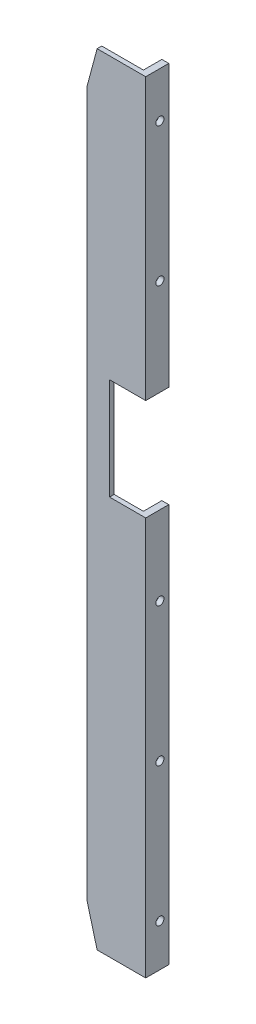
SolidWorks part; units mm, degrees
material "6061-T6 Al"
ref_plane "Front" through (0, 0, 0) normal (0, 0, 1) x (1, 0, 0)
ref_plane "Top" through (0, 0, 0) normal (0, 1, 0) x (1, 0, 0)
ref_plane "Right" through (0, 0, 0) normal (1, 0, 0) x (0, 0, -1)
sketch "MASS SEPARATION" plane through (0, 0, 0) normal (0, 0, 1) x (1, 0, 0)
  line L0 (334.7121, 0) -> (0, 0) construction
  line L1 (0, 0) -> (0, -602) construction
  line L2 (0, -602) -> (334.7121, -602) construction
  line L3 (163.2291, 47.5) -> (163.2291, -47.5)
  line L4 (163.2291, -554.5) -> (163.2291, -649.5)
  line L5 (-163.2291, -554.5) -> (-163.2291, -649.5)
  line L6 (-163.2291, 47.5) -> (-163.2291, -47.5)
  line L7 (168.2291, 47.5) -> (-168.2291, 47.5) construction
  line L8 (168.2291, 47.5) -> (168.2291, -649.5) construction
  line L9 (168.2291, -649.5) -> (-168.2291, -649.5) construction
  line L10 (-168.2291, -649.5) -> (-168.2291, 47.5) construction
  line L11 (0, -301) -> (297.114, -301) construction
  line L12 (-154.0291, -234.7) -> (-154.0291, -288.5)
  line L13 (6.2291, -234.7) -> (154.0291, -234.7)
  line L14 (6.2291, -234.7) -> (6.2291, -288.5)
  line L15 (6.2291, -288.5) -> (154.0291, -288.5)
  line L16 (154.0291, -234.7) -> (154.0291, -288.5)
  line L17 (-6.2291, -288.5) -> (-154.0291, -288.5)
  line L18 (-6.2291, -234.7) -> (-6.2291, -288.5)
  line L19 (-6.2291, -234.7) -> (-154.0291, -234.7)
  arc A0 (163.2291, 47.5) -> (-163.2291, 47.5) centre (0, 0) ccw
  arc A1 (163.2291, -554.5) -> (-163.2291, -554.5) centre (0, -602) ccw
  arc A2 (-163.2291, -47.5) -> (163.2291, -47.5) centre (0, 0) ccw
  arc A3 (-163.2291, -649.5) -> (163.2291, -649.5) centre (0, -602) ccw
  point P13 (168.2291, 47.5)
  point P14 (168.2291, -649.5)
  point P15 (-168.2291, 47.5)
  point P16 (-168.2291, -649.5)
  dimension "D2" = 170
  dimension "D1" = 602
  dimension "D3" = 95
  dimension "D4" = 12.5
  dimension "D5" = 5
  dimension "D6" = 301
  dimension "D7" = 5
  dimension "D8" = 147.8
  dimension "D9" = 162
  dimension "D10" = 53.8
  dimension "D11" = 301
  dimension "D12" = 234.7
  dimension "D13" = 326.4583
sketch "Sketch2" plane through (0, 0, 0) normal (0, 0, 1) x (1, 0, 0)
  line L0 (168.2291, 47.5) -> (168.2291, -47.5)
  line L1 (168.2291, 47.5) -> (204.0291, 47.5)
  line L2 (154.0291, -234.7) -> (154.0291, -288.5) construction
  line L3 (163.2291, 47.5) -> (163.2291, -47.5) construction
  line L4 (204.0291, 47.5) -> (204.0291, -649.5)
  line L5 (0, 0) -> (283.1149, 0) construction
  line L6 (334.7121, 0) -> (0, 0) construction
  line L7 (0, -602) -> (334.7121, -602) construction
  line L8 (168.2291, -554.5) -> (168.2291, -649.5)
  line L9 (168.2291, -649.5) -> (204.0291, -649.5)
  line L10 (159.0291, -81.8349) -> (159.0291, -520.1651)
  line L13 (168.2291, -47.5) -> (159.0291, -81.8349)
  line L14 (168.2291, -554.5) -> (159.0291, -520.1651)
  dimension "D1" = 47.5
  dimension "D2" = 5
  dimension "D3" = 45
  dimension "D4" = 5
  dimension "D5" = 47.5
  dimension "D6" = 47.5
  dimension "D7" = 15
  dimension "D8" = 47.5
  dimension "D9" = 15
  dimension "D10" = 697
extrude "Extrude1" add sketch "Sketch2" along normal mid plane 101.6
sketch "Sketch3" plane through (0, 0, 0) normal (0, 1, 0) x (1, 0, 0)
  line L1 (142.5291, 49.3) -> (202.5291, 49.3)
  line L2 (142.5291, 49.3) -> (142.5291, -49.3)
  line L3 (142.5291, -49.3) -> (202.5291, -49.3)
  line L4 (202.5291, 49.3) -> (202.5291, -49.3)
  line L5 (204.0291, 50.8) -> (168.2291, 50.8) construction
  line L6 (204.0291, -50.8) -> (204.0291, 50.8) construction
  line L7 (204.0291, -50.8) -> (168.2291, -50.8) construction
  dimension "D1" = 1.5
  dimension "D2" = 1.5
  dimension "D3" = 1.5
  dimension "D4" = 60
extrude "Cut-Extrude1" cut sketch "Sketch3" against normal through all and the other way through all
ref_plane "Plane1" through (0, -301, 0) normal (0, 1, 0) x (-1, 0, 0)
sketch "Sketch5" plane through (0, -301, 0) normal (0, 1, 0) x (1, 0, 0)
  line L0 (159.0291, 49.3) -> (159.0291, 50.8) construction
  line L1 (198.0291, 13.4125) -> (202.5291, 13.4125)
  line L2 (164.5291, 1.4125) -> (164.5291, -1.5875)
  line L3 (164.5291, -1.5875) -> (202.5291, -1.5875)
  line L4 (202.5291, 13.4125) -> (202.5291, -1.5875)
  line L6 (-163.2291, 0) -> (163.2291, 0) construction
  line L7 (202.5291, -49.3) -> (202.5291, 49.3) construction
  line L8 (198.0291, 13.4125) -> (198.0291, 1.4125)
  line L9 (198.0291, 1.4125) -> (164.5291, 1.4125)
  dimension "D1" = 15
  dimension "D2" = 38
  dimension "D3" = 1.5875
  dimension "D4" = 3
  dimension "D5" = 4.5
  dimension "D6" = 5.5
extrude "Extrude2" add sketch "Sketch5" along normal offset from surface 95 and the other way offset from surface (253.5 mm away) 95 separate body up to face at (185.7541, 47.5, 0) other way up to face at (185.7541, -649.5, 0)
sketch "Sketch11" plane through (0, 0, 0) normal (0, 0, 1) x (1, 0, 0)
  line L0 (170.9739, -47.5) -> (153.9591, -111)
  line L1 (153.9591, -111) -> (130.0291, -111)
  line L2 (130.0291, -111) -> (130.0291, -11)
  line L3 (170.9739, -47.5) -> (170.9739, -11)
  line L5 (170.9739, -11) -> (130.0291, -11)
  line L9 (23.4911, -301) -> (267.2307, -301) construction
  line L10 (0, -301) -> (297.114, -301) construction
  line L11 (153.9591, -491) -> (130.0291, -491)
  line L12 (170.9739, -554.5) -> (153.9591, -491)
  line L13 (170.9739, -554.5) -> (170.9739, -591)
  line L14 (170.9739, -591) -> (130.0291, -591)
  line L15 (130.0291, -491) -> (130.0291, -591)
  line L16 (159.0291, -81.8349) -> (159.0291, -520.1651) construction
  dimension "D1" = 290
  dimension "D2" = 100
  dimension "D3" = 29
  dimension "D4" = 23.93
extrude "Extrude8" cut sketch "Sketch11" against normal mid plane 150
sketch "Sketch4" plane through (0, 0, 0) normal (0, 0, 1) x (1, 0, 0)
  line L0 (159.0291, -81.8349) -> (159.0291, -520.1651) construction
  line L1 (209.0291, -229.7) -> (179.0291, -229.7)
  line L2 (209.0291, -229.7) -> (209.0291, -295.7)
  line L3 (209.0291, -295.7) -> (179.0291, -295.7)
  line L4 (179.0291, -229.7) -> (179.0291, -295.7)
  line L6 (164.5291, -71.5522) -> (164.5291, -530.4478) construction
  line L7 (6.2291, -234.7) -> (154.0291, -234.7) construction
  line L8 (6.2291, -288.5) -> (154.0291, -288.5) construction
  line L9 (204.0291, -649.5) -> (204.0291, 47.5) construction
  dimension "D1" = 5
  dimension "D2" = 7.2
  dimension "D3" = 5
  dimension "D4" = 20
  dimension "D5" = 66
  dimension "D6" = 14.5
extrude "Cut-Extrude2" cut sketch "Sketch4" against normal mid plane 92
sketch "Sketch7" plane through (0, 0, 0) normal (0, 0, 1) x (1, 0, 0)
  line L0 (159.0291, -81.8349) -> (159.0291, -520.1651) construction
  line L1 (129.0291, -157.5) -> (179.0291, -157.5)
  line L2 (129.0291, -157.5) -> (129.0291, -197.5)
  line L3 (129.0291, -197.5) -> (179.0291, -197.5)
  line L4 (179.0291, -157.5) -> (179.0291, -197.5)
  line L5 (129.0291, -414.5) -> (179.0291, -414.5)
  line L6 (129.0291, -414.5) -> (129.0291, -454.5)
  line L7 (129.0291, -454.5) -> (179.0291, -454.5)
  line L8 (179.0291, -414.5) -> (179.0291, -454.5)
  line L11 (168.2291, -649.5) -> (204.0291, -649.5) construction
  line L13 (204.0291, 47.5) -> (168.2291, 47.5) construction
  dimension "D1" = 20
  dimension "D2" = 50
  dimension "D3" = 40
  dimension "D4" = 40
  dimension "D5" = 235
  dimension "D6" = 245
  dimension "D7" = 20
extrude "Extrude4" [suppressed] cut sketch "Sketch7" against normal mid plane 150
sketch "Sketch8" plane through (0, 0, -50.8) normal (0, 0, -1) x (-1, 0, 0)
  line L0 (-227.5077, -262.7) -> (-137.1127, -262.7) construction
  line L1 (-204.0291, 47.5) -> (-168.2291, 47.5) construction
  line L2 (-204.0291, -649.5) -> (-204.0291, 47.5) construction
  circle A0 centre (-190.8541, -239.7) radius 2.25
  circle A1 centre (-190.8541, -285.7) radius 2.25
  dimension "D1" = 4.5
  dimension "D2" = 310.2
  dimension "D3" = 23
  dimension "D4" = 287.2
  dimension "D5" = 46
  dimension "D6" = 13.175
extrude "Extrude5" [suppressed] cut sketch "Sketch8" against normal through all
sketch "Sketch9" plane through (204.0291, 0, 0) normal (1, 0, 0) x (0, 0, -1)
  line L0 (-50.8, -649.5) -> (-50.8, 47.5) construction
  line L1 (50.8, -649.5) -> (50.8, 47.5) construction
  line L2 (-50.8, 47.5) -> (50.8, 47.5) construction
  line L3 (46, -295.7) -> (-46, -295.7) construction
  circle A0 centre (-17.8, -317.5) radius 2.25
  circle A1 centre (17.8, -317.5) radius 2.25
  dimension "D2" = 4.5
  dimension "D1" = 35.6
  dimension "D3" = 33
  dimension "D4" = 33
  dimension "D5" = 365
  dimension "D6" = 21.8
extrude "Extrude6" [suppressed] cut sketch "Sketch9" against normal through all
sketch "Sketch6" plane through (198.0291, 0, 0) normal (-1, 0, 0) x (0, 0, 1)
  line L1 (-13.4125, -47.5) -> (-13.4125, -229.7) construction
  line L2 (1.5875, -71.5522) -> (1.5875, -530.4478) construction
  line L3 (49.3, 47.5) -> (-49.3, 47.5) construction
  line L4 (-1.4125, -47.5) -> (-13.4125, -47.5) construction
  line L5 (-1.4125, -47.5) -> (-1.4125, -229.7) construction
  circle A0 centre (-6.4125, -77.5) radius 2.25
  circle A1 centre (-6.4125, -77.5) radius 4.11 construction
  dimension "D1" = 4.5
  dimension "D2" = 8.22
  dimension "D3" = 5
  dimension "D4" = 7
  dimension "D5" = 8
  dimension "D6" = 125
  dimension "D7" = 30
hole_wizard "Tapped Hole for #8-32 Helicoil1" positions "3DSketch2" profile "Sketch34" tap size "#8-32" standard "Helicoil® Inch" end condition through all
sketch3d "3DSketch2"
  point P1 (204.0291, -77.0111, -7.6402)
sketch "Sketch34" plane through (204.0291, -77.0111, -7.6402) normal (0, 1, 0) x (0, 0, -1)
  line L0 (0, 0) -> (0, 45)
  line L1 (0, 45) -> (2.1971, 45)
  line L3 (2.1971, 45) -> (2.1971, 5)
  line L4 (2.1971, 5) -> (2.6378, 5)
  line L5 (2.6378, 5) -> (2.6378, 0)
  line L7 (2.6378, 0) -> (0, 0)
  line L11 (0, -6.35) -> (0, 107.95) construction
  dimension "Thru Tap Drill Dia." = 4.3942
  dimension "Thru Tap Drill Depth" = 45
  dimension "Thread Major Dia." = 5.2756
  dimension "Thread Depth" = 5
pattern_linear "LPattern1" count 6 spacing 90 along (0, -1, 0) skipping (2, 0) of "Tapped Hole for #8-32 Helicoil1"
sketch "Sketch10" plane through (0, 0, 50.8) normal (0, 0, 1) x (1, 0, 0)
  line L0 (204.0291, -649.5) -> (204.0291, 47.5) construction
  line L1 (181.8041, -95) -> (204.0291, -95) construction
  line L2 (181.8041, -95) -> (181.8041, -125) construction
  line L3 (181.8041, -125) -> (204.0291, -125) construction
  line L4 (204.0291, -95) -> (204.0291, -125) construction
  line L5 (181.8041, -335) -> (204.0291, -335) construction
  line L6 (177.683, -110) -> (206.6192, -110) construction
  line L7 (204.0291, 47.5) -> (168.2291, 47.5) construction
  line L8 (204.0291, -305) -> (204.0291, -335) construction
  line L9 (181.8041, -305) -> (204.0291, -305) construction
  line L10 (181.8041, -305) -> (181.8041, -335) construction
  line L11 (177.683, -320) -> (206.6192, -320) construction
  line L12 (181.8041, -20) -> (204.0291, -20) construction
  line L13 (181.8041, -20) -> (181.8041, -50) construction
  line L14 (177.683, -35) -> (206.6192, -35) construction
  line L15 (181.8041, -50) -> (204.0291, -50) construction
  line L16 (204.0291, -20) -> (204.0291, -50) construction
  line L17 (181.8041, -609) -> (204.0291, -609) construction
  line L18 (177.683, -594) -> (206.6192, -594) construction
  line L19 (181.8041, -579) -> (204.0291, -579) construction
  line L20 (181.8041, -579) -> (181.8041, -609) construction
  line L21 (204.0291, -579) -> (204.0291, -609) construction
  circle A0 centre (192.8541, -102.5) radius 2.25
  circle A1 centre (192.8541, -117.5) radius 2.25
  circle A2 centre (192.8541, -327.5) radius 2.25
  circle A3 centre (192.8541, -312.5) radius 2.25
  circle A4 centre (192.8541, -42.5) radius 2.25
  circle A5 centre (192.8541, -27.5) radius 2.25
  circle A6 centre (192.8541, -586.5) radius 2.25
  circle A7 centre (192.8541, -601.5) radius 2.25
  dimension "D4" = 4.5
  dimension "D11" = 274
  dimension "D1" = 157.5
  dimension "D2" = 30
  dimension "D3" = 22.225
  dimension "D5" = 15
  dimension "D6" = 7.5
  dimension "D7" = 7.5
  dimension "D8" = 11.175
  dimension "D9" = 210
  dimension "D10" = 82.5
extrude "Extrude7" cut sketch "Sketch10" against normal through all
sketch "Sketch12" [suppressed] plane through (0, 0, 0) normal (0, 1, 0) x (1, 0, 0)
  line L0 (200.7791, -47.55) -> (200.7791, 47.55) construction
  line L1 (159.0291, 47.55) -> (200.7791, 47.55)
  line L2 (159.0291, 47.55) -> (159.0291, -47.55)
  line L3 (159.0291, -47.55) -> (200.7791, -47.55)
  line L4 (200.7791, 47.55) -> (200.7791, -47.55)
  line L5 (200.7791, 47.55) -> (168.2291, 47.55) construction
  line L6 (168.2291, -47.55) -> (200.7791, -47.55) construction
  line L7 (159.0291, 47.55) -> (159.0291, 50.8) construction
extrude "Extrude9" [suppressed] cut sketch "Sketch12" against normal blind 600
sketch "Sketch13" plane through (0, 0, 0) normal (0, 1, 0) x (1, 0, 0)
  line L0 (202.5291, -49.3) -> (202.5291, 49.3) construction
  line L1 (164.5291, 13.4125) -> (202.5291, 13.4125)
  line L2 (164.5291, 13.4125) -> (164.5291, -1.5875)
  line L3 (164.5291, -1.5875) -> (202.5291, -1.5875)
  line L4 (202.5291, 13.4125) -> (202.5291, -1.5875)
  line L5 (202.5291, -1.5875) -> (170.9739, -1.5875) construction
  line L6 (164.5291, -1.5875) -> (164.5291, 1.4125) construction
  line L7 (198.0291, 13.4125) -> (202.5291, 13.4125) construction
  line L8 (104.5291, 73.4125) -> (262.5291, 73.4125)
  line L9 (262.5291, 73.4125) -> (262.5291, -61.5875)
  line L10 (104.5291, -61.5875) -> (262.5291, -61.5875)
  line L11 (104.5291, 73.4125) -> (104.5291, -61.5875)
  dimension "D1" = 60
extrude "Extrude10" cut sketch "Sketch13" against normal blind 700 and the other way blind 100
sketch "Sketch20" [suppressed] plane through (0, 0, 50.8) normal (0, 0, 1) x (1, 0, 0)
  circle A0 centre (179.0291, -197.5) radius 7.5
  dimension "D1" = 15
extrude "Extrude17" [suppressed] cut sketch "Sketch20" against normal blind 10
fillet "Fillet1" [suppressed] radius 2.5
mirror "Mirror2" [suppressed] about plane through (0, 0, 0) normal (0, 0, 1)
hole_wizard "#8-32 Tapped Hole1" positions "Sketch24" profile "Sketch25" tap size "#8-32" standard "Ansi Inch"
sketch "Sketch24" plane through (204.0291, 0, 0) normal (1, 0, 0) x (0, 0, -1)
  line L0 (-50.8, 47.5) -> (50.8, 47.5) construction
  line L1 (0, 47.5) -> (0, 0) construction
  point P0 (-40, 37.5)
  point P1 (40, 37.5)
  dimension "D1" = 10
  dimension "D2" = 40
sketch "Sketch25" plane through (204.0291, 37.5, 40) normal (0, 1, 0) x (0, 0, -1)
  line L0 (0, 0) -> (0, 45)
  line L1 (0, 45) -> (1.7272, 45)
  line L2 (1.7272, 45) -> (1.7272, 0)
  line L5 (1.7272, 0) -> (0, 0)
  line L11 (0, -6.35) -> (0, 107.95) construction
  dimension "Thru Tap Drill Dia." = 3.4544
  dimension "Thru Tap Drill Depth" = 45
cosmetic thread "Hole Thread1" [suppressed] parameters "D1"=3.25, "D2"=4.1656
cosmetic thread "Hole Thread2" [suppressed] parameters "D1"=3.25, "D2"=4.1656
ref_plane "Plane2" [suppressed] through (0, 0, -50.8) normal (0, 0, -1) x (-1, 0, 0)
sketch "Sketch31" [suppressed] plane through (0, 0, -50.8) normal (0, 0, -1) x (-1, 0, 0)
  line L0 (-179.0291, -414.5) -> (-159.0291, -414.5) construction
  line L1 (-204.0291, -383) -> (-193.5291, -383)
  line L2 (-204.0291, -383) -> (-204.0291, -397)
  line L3 (-204.0291, -397) -> (-193.5291, -397)
  line L4 (-189.0291, -387.5) -> (-189.0291, -392.5)
  line L5 (-204.0291, -649.5) -> (-204.0291, 47.5) construction
  arc A0 (-189.0291, -387.5) -> (-193.5291, -383) centre (-193.5291, -387.5) ccw
  arc A1 (-193.5291, -397) -> (-189.0291, -392.5) centre (-193.5291, -392.5) ccw
  point P10 (-189.0291, -383)
  point P13 (-189.0291, -397)
  dimension "D5" = 4.5
  dimension "D1" = 14
  dimension "D2" = 17.5
  dimension "D3" = 15
  dimension "D4" = 0
extrude "Cut-Extrude3" [suppressed] cut sketch "Sketch31" against normal blind 22.5
